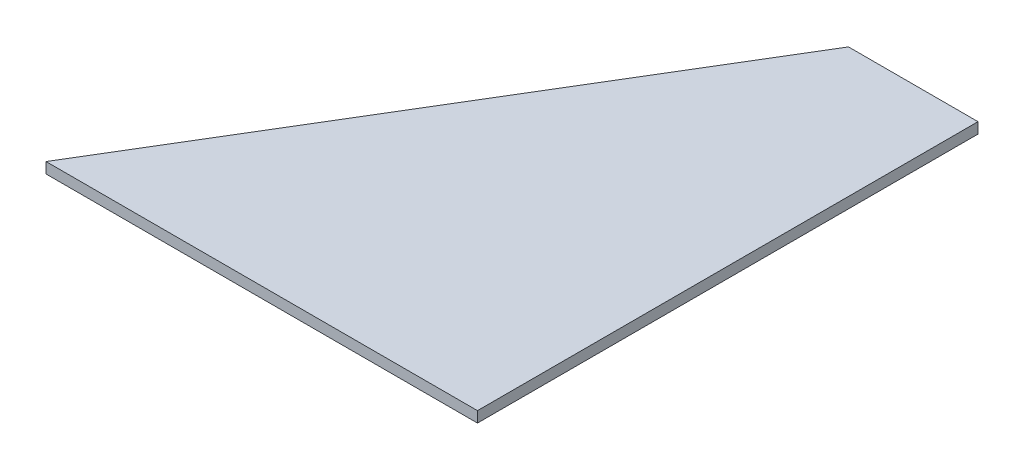
SolidWorks part; units mm, degrees
material "Balsa"
ref_plane "Front Plane" through (0, 0, 0) normal (0, 0, 1) x (1, 0, 0)
ref_plane "Top Plane" through (0, 0, 0) normal (0, 1, 0) x (1, 0, 0)
ref_plane "Right Plane" through (0, 0, 0) normal (1, 0, 0) x (0, 0, -1)
sketch "Sketch1" plane through (0, 0, 0) normal (0, 1, 0) x (1, 0, 0)
  line L0 (0, 0) -> (0, 147.32)
  line L1 (0, 147.32) -> (-38.1, 147.32)
  line L2 (-38.1, 147.32) -> (-127, 0)
  line L3 (-127, 0) -> (0, 0)
  dimension "D1" = 127
  dimension "D2" = 147.32
  dimension "D3" = 38.1
extrude "Boss-Extrude1" add sketch "Sketch1" along normal blind 3.175
